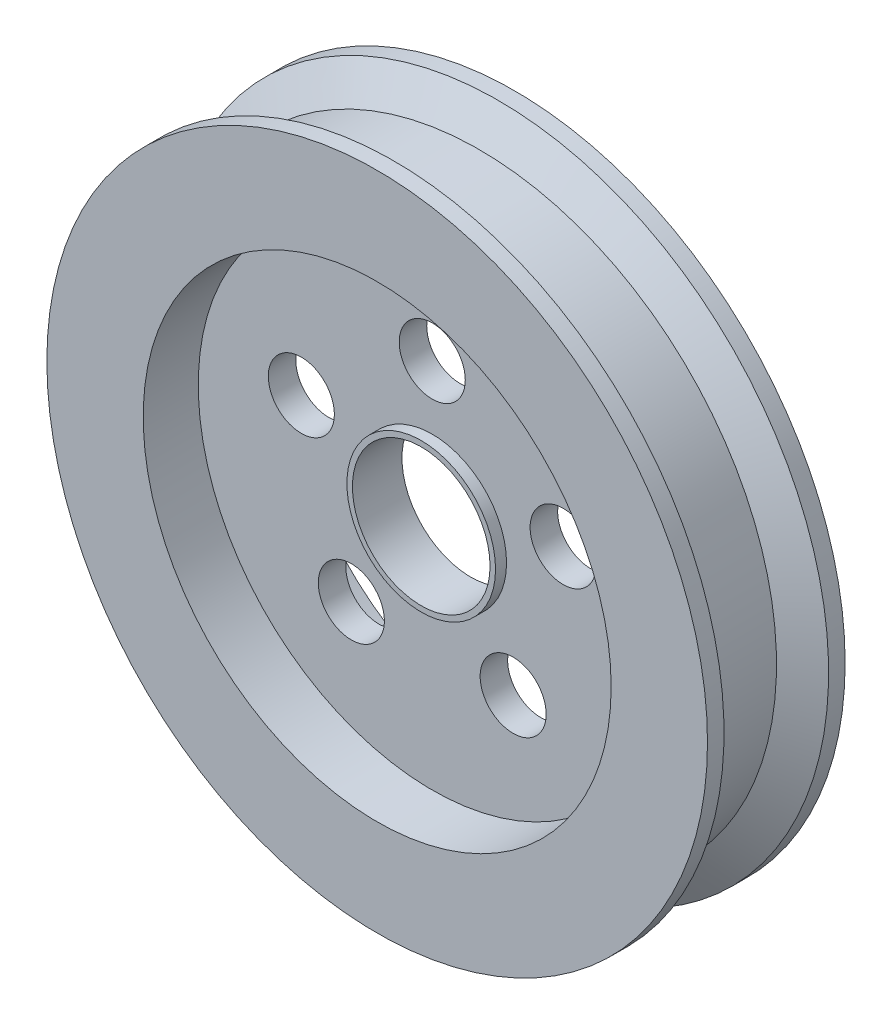
SolidWorks part; units mm, degrees
ref_plane "Front Plane" through (0, 0, 0) normal (0, 0, 1) x (1, 0, 0)
ref_plane "Top Plane" through (0, 0, 0) normal (0, 1, 0) x (1, 0, 0)
ref_plane "Right Plane" through (0, 0, 0) normal (1, 0, 0) x (0, 0, -1)
sketch "Sketch1" plane through (0, 0, 0) normal (0, 0, 1) x (1, 0, 0)
  circle A0 centre (0, 0) radius 60
  circle A1 centre (0, 0) radius 12.5
  dimension "D1" = 120
  dimension "D2" = 25
extrude "Boss-Extrude1" add sketch "Sketch1" along normal mid plane 25
sketch "Sketch2" plane through (0, 0, 12.5) normal (0, 0, 1) x (1, 0, 0)
  circle A0 centre (0, 0) radius 42.5
  dimension "D1" = 85
extrude "Cut-Extrude1" cut sketch "Sketch2" against normal blind 10
mirror "Mirror1" about plane through (0, 0, 0) normal (0, 0, 1) of "Cut-Extrude1"
sketch "Sketch3" plane through (0, 0, 2.5) normal (0, 0, 1) x (1, 0, 0)
  circle A0 centre (0, 25) radius 6
  dimension "D2" = 12
  dimension "D1" = 25
extrude "Cut-Extrude2" cut sketch "Sketch3" against normal through all
pattern_circular "CirPattern1" count 5 over 360 about axis through (0, 0, 0) along (0, 0, 1) of "Cut-Extrude2"
sketch "Sketch4" plane through (0, 0, 0) normal (0, 1, 0) x (1, 0, 0)
  line L0 (0, 27.8149) -> (0, -23.4181) construction
  line L1 (60, 9.5) -> (54, 6.0359)
  line L2 (60, -12.5) -> (60, 12.5) construction
  line L3 (54, 6.0359) -> (54, -6.0359)
  line L4 (54, -6.0359) -> (60, -9.5)
  line L5 (60, -9.5) -> (60, 9.5)
  dimension "D1" = 6
  dimension "D2" = 3
  dimension "D3" = 3
  dimension "D4" = 60
  dimension "D5" = 60
revolve "Cut-Revolve1" cut sketch "Sketch4" angle 360 about L0
sketch "Sketch5" plane through (0, 0, 2.5) normal (0, 0, 1) x (1, 0, 0)
  circle A0 centre (0, 0) radius 13.5
  circle A1 centre (0, 0) radius 12.5 construction
  circle A2 centre (0, 0) radius 12.5
  dimension "D1" = 27
extrude "Boss-Extrude2" add sketch "Sketch5" along normal blind 2 and the other way blind 7
